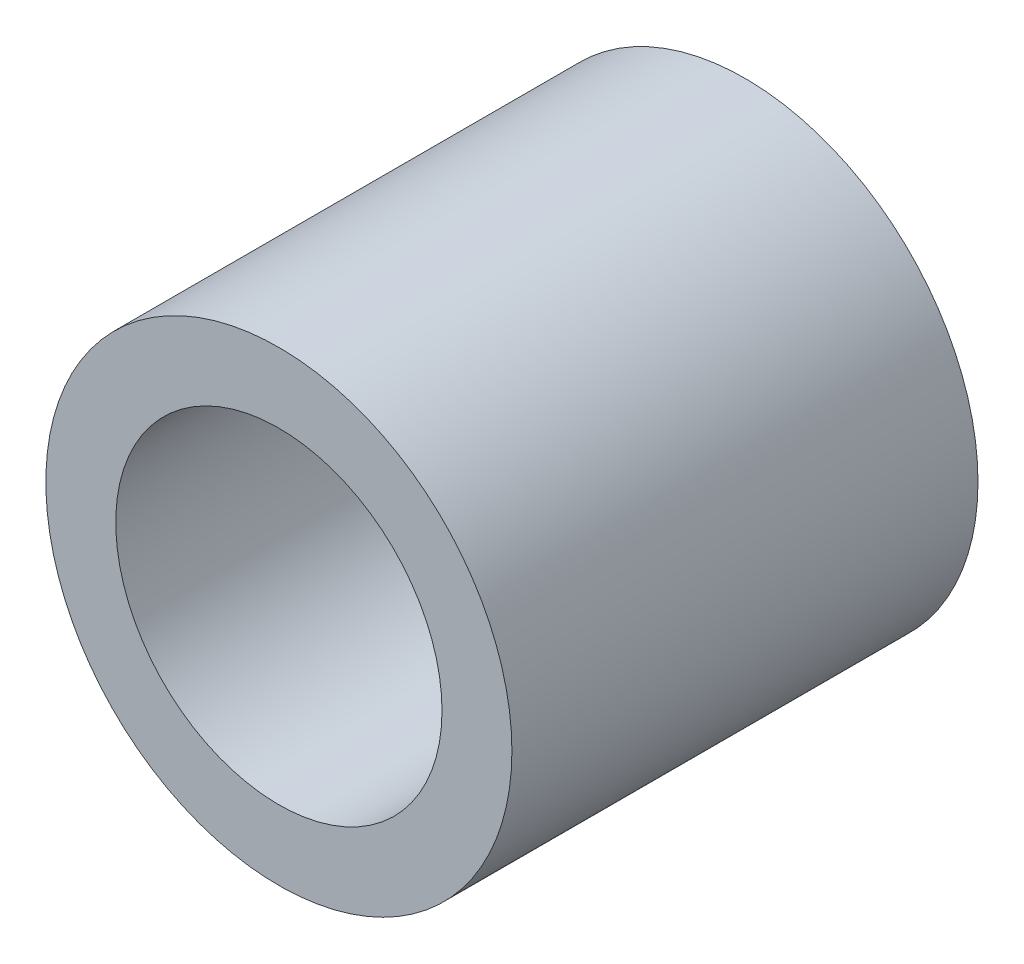
SolidWorks part; units mm, degrees
ref_plane "Front Plane" through (0, 0, 0) normal (0, 0, 1) x (1, 0, 0)
ref_plane "Top Plane" through (0, 0, 0) normal (0, 1, 0) x (1, 0, 0)
ref_plane "Right Plane" through (0, 0, 0) normal (1, 0, 0) x (0, 0, -1)
sketch "Sketch1" plane through (0, 0, 0) normal (0, 0, 1) x (1, 0, 0)
  circle A0 centre (0, 0) radius 10
  dimension "D1" = 20
extrude "Boss-Extrude1" add sketch "Sketch1" along normal blind 20 contours A0
sketch "Sketch2" plane through (0, 0, 0) normal (0, 0, 1) x (1, 0, 0)
  circle A0 centre (0, 0) radius 7
  dimension "D1" = 14
extrude "Cut-Extrude1" cut sketch "Sketch2" along normal blind 35
